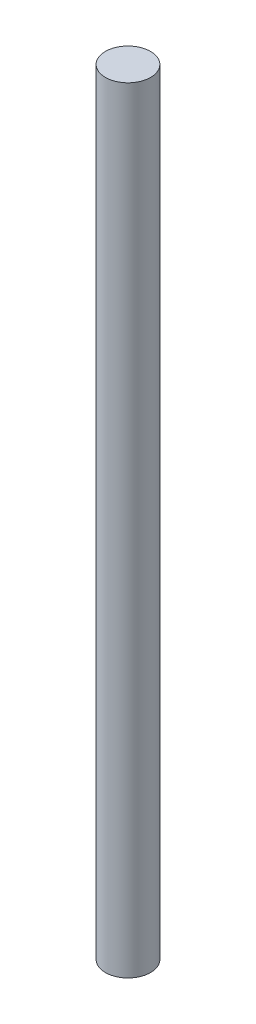
SolidWorks part; units mm, degrees
ref_plane "Alzado" through (0, 0, 0) normal (0, 0, 1) x (1, 0, 0)
ref_plane "Planta" through (0, 0, 0) normal (0, 1, 0) x (1, 0, 0)
ref_plane "Vista lateral" through (0, 0, 0) normal (1, 0, 0) x (0, 0, -1)
sketch "Croquis1" plane through (0, 0, 0) normal (0, 1, 0) x (1, 0, 0)
  circle A0 centre (0, 0) radius 3.2
  dimension "D1" = 6.4
extrude "Saliente-Extruir1" add sketch "Croquis1" along normal blind 110
